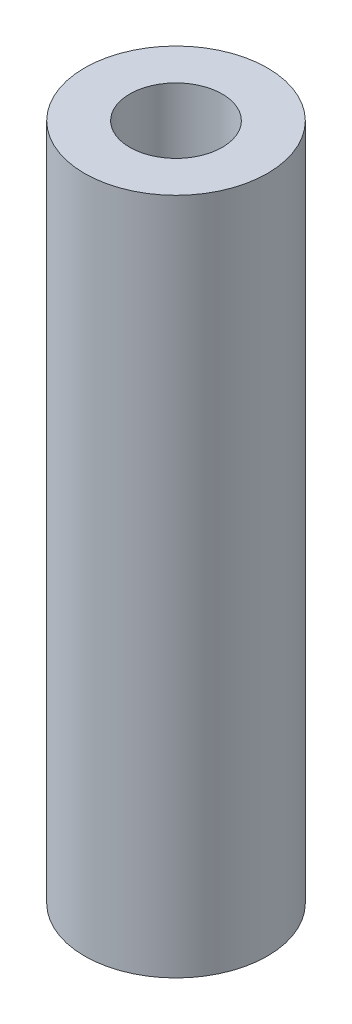
SolidWorks part; units mm, degrees
ref_plane "Front Plane" through (0, 0, 0) normal (0, 0, 1) x (1, 0, 0)
ref_plane "Top Plane" through (0, 0, 0) normal (0, 1, 0) x (1, 0, 0)
ref_plane "Right Plane" through (0, 0, 0) normal (1, 0, 0) x (0, 0, -1)
sketch "Sketch1" plane through (0, 0, 0) normal (0, 1, 0) x (1, 0, 0)
  circle A0 centre (0, 0) radius 2.6
  circle A1 centre (0, 0) radius 5.14
  dimension "D1" = 5.2
  dimension "D2" = 2.54
extrude "Boss-Extrude1" add sketch "Sketch1" along normal blind 38.1
